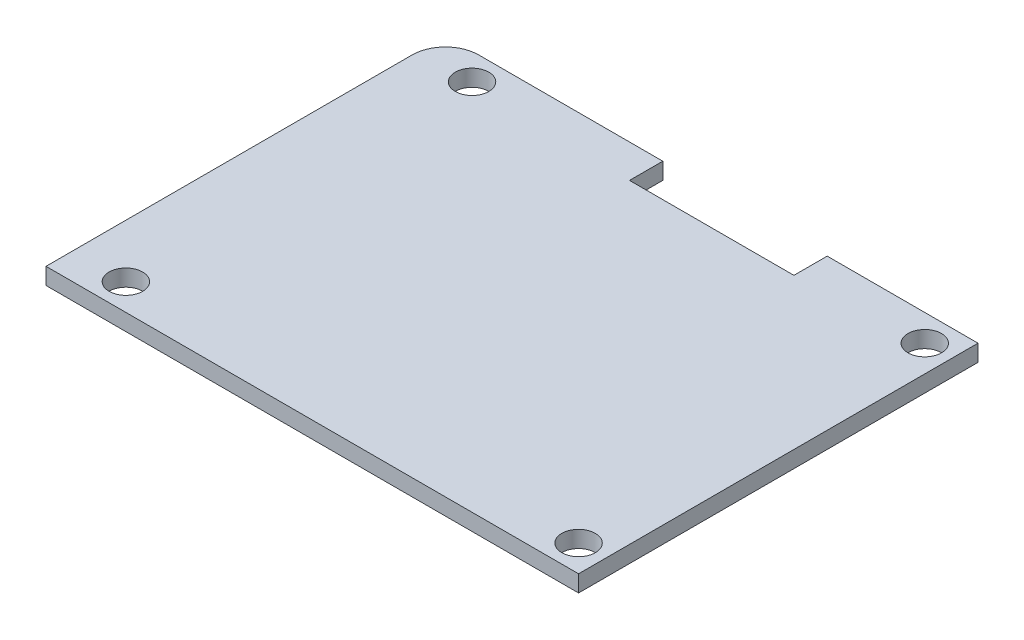
SolidWorks part; units mm, degrees
material "A-Glass Fiber"
ref_plane "Front Plane" through (0, 0, 0) normal (0, 0, 1) x (1, 0, 0)
ref_plane "Top Plane" through (0, 0, 0) normal (0, 1, 0) x (1, 0, 0)
ref_plane "Right Plane" through (0, 0, 0) normal (1, 0, 0) x (0, 0, -1)
sketch "Sketch1" plane through (0, 0, 0) normal (0, 1, 0) x (1, 0, 0)
  line L0 (36.416, 38.1) -> (50.8, 38.1)
  line L1 (0, 0) -> (50.8, 0)
  line L2 (0, 0) -> (0, 38.1)
  line L3 (0, 38.1) -> (20.734, 38.1)
  line L4 (50.8, 0) -> (50.8, 38.1)
  line L6 (20.734, 38.1) -> (20.734, 34.925)
  line L7 (20.734, 34.925) -> (36.416, 34.925)
  line L8 (36.416, 38.1) -> (36.416, 34.925)
  dimension "D1" = 20.734
  dimension "D2" = 36.416
  dimension "D3" = 50.8
  dimension "D4" = 38.1
  dimension "D5" = 3.175
extrude "Boss-Extrude1" add sketch "Sketch1" along normal blind 1.5875
sketch "Sketch2" plane through (0, 1.5875, 0) normal (0, 1, 0) x (1, 0, 0)
  line L0 (0, 38.1) -> (0, 0) construction
  line L1 (0, 0) -> (50.8, 0) construction
  circle A0 centre (5.08, 35.56) radius 1.6
  circle A1 centre (48.26, 2.54) radius 1.6
  circle A2 centre (48.26, 35.56) radius 1.6
  circle A3 centre (5.08, 2.54) radius 1.6
  point P12 (0, 0)
  point P13 (0, 0)
  point P14 (0, 0)
  point P15 (0, 0)
  dimension "D1" = 3.2
  dimension "D2" = 5.08
  dimension "D3" = 2.54
  dimension "D5" = 48.26
  dimension "D6" = 35.56
extrude "Cut-Extrude1" cut sketch "Sketch2" against normal through all
fillet "Fillet1" radius 3.175 1 edges at (0, 0.7937, -38.1)
